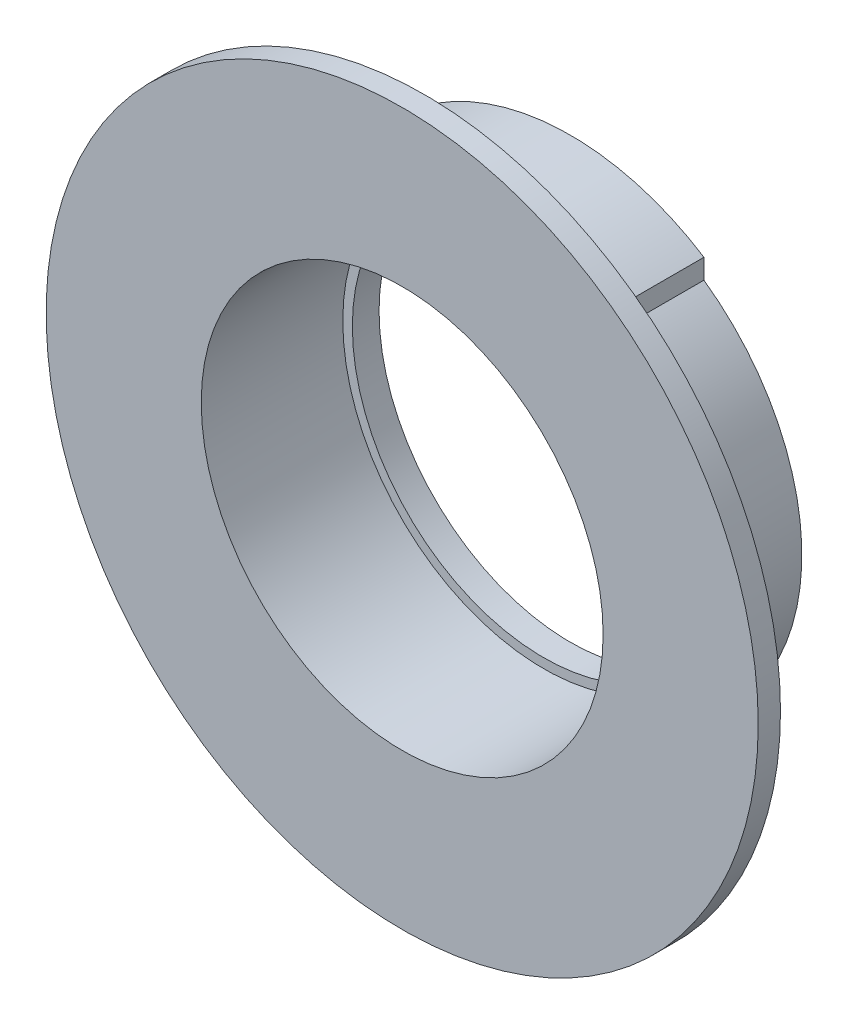
SolidWorks part; units mm, degrees
ref_plane "Front Plane" through (0, 0, 0) normal (0, 0, 1) x (1, 0, 0)
ref_plane "Top Plane" through (0, 0, 0) normal (0, 1, 0) x (1, 0, 0)
ref_plane "Right Plane" through (0, 0, 0) normal (1, 0, 0) x (0, 0, -1)
sketch "Sketch1" plane through (0, 0, 0) normal (0, 0, 1) x (1, 0, 0)
  circle A0 centre (0, 0) radius 27.85
  circle A1 centre (0, 0) radius 22.575
  dimension "D1" = 55.7
  dimension "D2" = 45.15
extrude "Boss-Extrude1" add sketch "Sketch1" along normal blind 16.4
sketch "Sketch2" plane through (0, 0, 16.4) normal (0, 0, 1) x (1, 0, 0)
  circle A0 centre (0, 0) radius 22.575
  circle A1 centre (0, 0) radius 40
  circle A2 centre (0, 0) radius 22.575 construction
  dimension "D1" = 80
extrude "Boss-Extrude2" add sketch "Sketch2" along normal blind 2.5
sketch "Sketch3" plane through (0, 0, 0) normal (0, 0, -1) x (-1, 0, 0)
  circle A0 centre (0, 0) radius 21.5
  circle A1 centre (0, 0) radius 22.575
  circle A2 centre (0, 0) radius 22.575 construction
  dimension "D1" = 43
extrude "Boss-Extrude3" add sketch "Sketch3" against normal blind 3
sketch "Sketch4" plane through (0, 0, 0) normal (0, 0, -1) x (-1, 0, 0)
  line L1 (15, 27.85) -> (-15, 27.85)
  line L2 (15, 27.85) -> (15, -27.85)
  line L3 (15, -27.85) -> (-15, -27.85)
  line L4 (-15, 27.85) -> (-15, -27.85)
  line L5 (15, 27.85) -> (-15, -27.85) construction
  line L6 (15, -27.85) -> (-15, 27.85) construction
  circle A0 centre (0, 0) radius 26
  circle A1 centre (0, 0) radius 27.85
  circle A2 centre (0, 0) radius 27.85 construction
  circle M7 centre (0, 0) radius 27.85
  dimension "D1" = 52
  dimension "D2" = 30
extrude "Cut-Extrude1" cut sketch "Sketch4" against normal up to surface (16.4 mm away) contours A0 L4 M7 | A0 L2 M7 up to face at (27.85, 0, 16.4)
